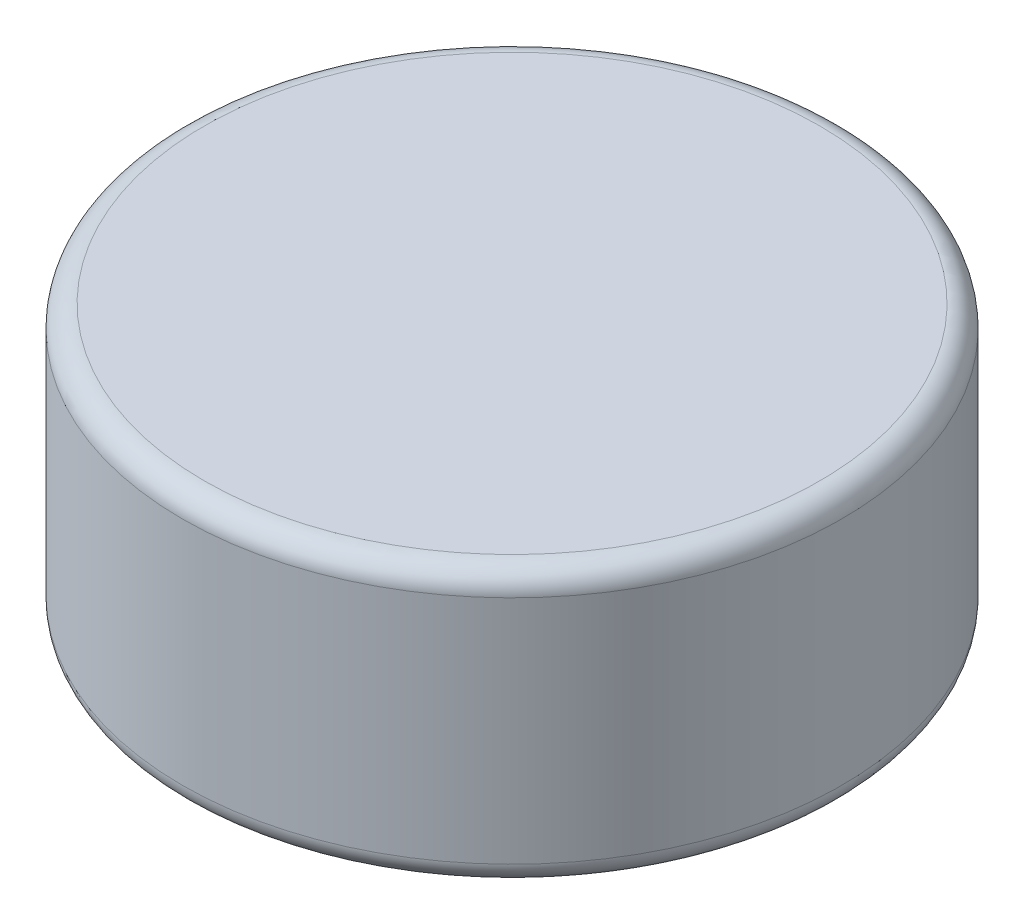
SolidWorks part; units mm, degrees
ref_plane "Front" through (0, 0, 0) normal (0, 0, 1) x (1, 0, 0)
ref_plane "Top" through (0, 0, 0) normal (0, 1, 0) x (1, 0, 0)
ref_plane "Right" through (0, 0, 0) normal (1, 0, 0) x (0, 0, -1)
sketch "草图1" plane through (0, 0, 0) normal (0, 1, 0) x (1, 0, 0)
  circle A0 centre (0, 0) radius 3
extrude "凸台-拉伸1" add sketch "草图1" along normal blind 2.5 contours A0
fillet "圆角1" radius 0.2 2 edges at (0, 0, 3) (0, 2.5, 3)
